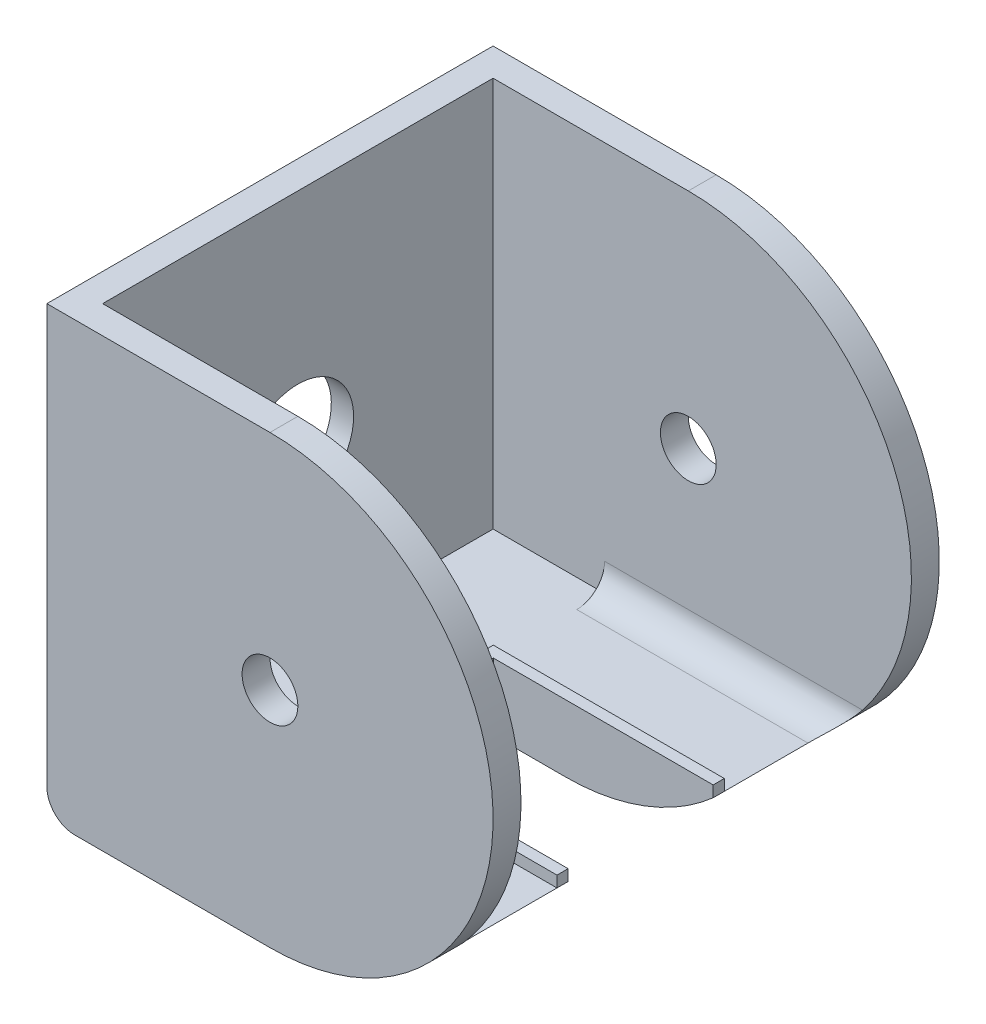
SolidWorks part; units mm, degrees
material "Custom Plastic"
ref_plane "Front Plane" through (0, 0, 0) normal (0, 0, 1) x (1, 0, 0)
ref_plane "Top Plane" through (0, 0, 0) normal (0, 1, 0) x (1, 0, 0)
ref_plane "Right Plane" through (0, 0, 0) normal (1, 0, 0) x (0, 0, -1)
sketch "Sketch1" plane through (0, 0, 0) normal (0, 0, 1) x (1, 0, 0)
  line L0 (72.2954, 0) -> (-7.7046, 0)
  line L1 (-7.7046, -40) -> (32.2954, -40)
  line L2 (-7.7046, -40) -> (-7.7046, 40)
  line L3 (-7.7046, 40) -> (32.2954, 40)
  line L5 (0, 0) -> (-7.7029, 0.3675) construction
  line L6 (0, 0) -> (-7.7029, -0.3675) construction
  arc A0 (-7.7029, 0.3675) -> (-7.7029, -0.3675) centre (32.2954, 0) ccw
  arc A1 (32.2954, -40) -> (32.2954, 40) centre (32.2954, 0) ccw
  circle A2 centre (32.2954, 0) radius 5
  point P0 (0, 0)
  dimension "D3" = 10
  dimension "D1" = 80
  dimension "D2" = 80
extrude "Boss-Extrude1" add sketch "Sketch1" along normal blind 5
sketch "Sketch2" plane through (0, 0, 5) normal (0, 0, 1) x (1, 0, 0)
  line L0 (-7.7046, 40) -> (-2.7046, 40)
  line L1 (-7.7046, 40) -> (32.2954, 40) construction
  line L2 (-2.7046, 40) -> (-2.7046, -40)
  line L3 (-7.7046, -40) -> (32.2954, -40) construction
  line L4 (-2.7046, -40) -> (-7.7046, -40)
  line L5 (-7.7046, -40) -> (-7.7046, 40)
  dimension "D1" = 5
extrude "Boss-Extrude2" add sketch "Sketch2" along normal blind 70
ref_plane "Plane1" through (0, 0, 40) normal (0, 0, 1) x (1, 0, 0)
mirror "Mirror1" about plane through (0, 0, 40) normal (0, 0, 1) of "Boss-Extrude1"
sketch "Sketch4" plane through (0, 0, 5) normal (0, 0, 1) x (1, 0, 0)
  line L0 (-2.7046, -40) -> (-2.7046, -30)
  line L1 (-2.7046, -40) -> (-2.7046, 40) construction
  line L2 (-2.7046, -30) -> (43.4973, -30)
  line L3 (43.4973, -30) -> (58.7529, -30)
  line L4 (-2.7046, -40) -> (32.2954, -40)
  arc A2 (32.2954, -40) -> (58.7529, -30) centre (32.2954, 0) ccw
  dimension "D1" = 10
extrude "Boss-Extrude3" add sketch "Sketch4" along normal blind 70
sketch "Sketch5" plane through (-7.7046, 0, 0) normal (-1, 0, 0) x (0, 0, 1)
  line L0 (0, 40) -> (80, -40)
  circle A0 centre (40, 0) radius 10
  dimension "D1" = 20
extrude "Cut-Extrude1" cut sketch "Sketch5" against normal blind 5 contours L0 A0 | L0 A0
sketch "Sketch6" plane through (-7.7046, 0, 0) normal (-1, 0, 0) x (0, 0, 1)
  circle A0 centre (40, 0) radius 20
  dimension "D1" = 40
extrude "Cut-Extrude2" cut sketch "Sketch6" against normal blind 1
sketch "Sketch7" plane through (0, -30, 0) normal (0, 1, 0) x (1, 0, 0)
  line L1 (-2.7046, -75) -> (-2.7046, -5) construction
  line L2 (58.7529, -75) -> (58.7529, -5) construction
  line L3 (58.7529, -40) -> (58.7529, -27)
  line L4 (58.7529, -27) -> (-2.7046, -27)
  line L5 (-2.7046, -27) -> (-2.7046, -40)
  line L6 (-2.7046, -40) -> (-2.7046, -53)
  line L7 (-2.7046, -53) -> (58.7529, -53)
  line L8 (58.7529, -53) -> (58.7529, -40)
  line L9 (19.3397, -53) -> (19.3397, -27)
  line M10 (58.7529, -75) -> (58.7529, -5)
  dimension "D1" = 13
  dimension "D2" = 13
extrude "Cut-Extrude3" cut sketch "Sketch7" against normal blind 19 contours L9 L7 L4 M10
sketch "Sketch8" plane through (0, -30, 0) normal (0, 1, 0) x (1, 0, 0)
  line L0 (58.7529, -53) -> (19.3397, -53)
  line L1 (19.3397, -53) -> (19.3397, -27)
  line L2 (19.3397, -27) -> (58.7529, -27)
  line L3 (58.7529, -27) -> (58.7529, -25)
  line L5 (58.7529, -55) -> (17.3397, -55)
  line L6 (17.3397, -55) -> (17.3397, -25)
  line L7 (17.3397, -25) -> (56.7529, -25)
  line L8 (58.7529, -55) -> (58.7529, -53)
  line L9 (56.7529, -25) -> (58.7529, -25)
  line L10 (58.7529, -27) -> (58.7529, -24.2721) construction
  line L11 (56.7529, -25) -> (56.7529, -24.2721) construction
  dimension "D1" = 2
extrude "Boss-Extrude4" add sketch "Sketch8" along normal blind 2
fillet "Fillet1" radius 5 3 edges at (-7.7046, -40, 40) (28.0241, -30, 5) (28.0241, -30, 75)
sketch "Sketch9" plane through (0, -30, 0) normal (0, 1, 0) x (1, 0, 0)
  line L0 (-2.7046, -70) -> (-2.7046, -5)
  line L1 (-2.7046, -5) -> (17.2954, -5)
  line L2 (-2.7046, -5) -> (32.2954, -5) construction
  line L3 (17.2954, -5) -> (17.2954, -75)
  line L4 (-2.7046, -70) -> (-2.7046, -75)
  line L5 (-2.7046, -75) -> (17.2954, -75)
  dimension "D1" = 20
extrude "Cut-Extrude4" cut sketch "Sketch9" along normal blind 27
sketch "Sketch10" plane through (0, -30, 0) normal (0, 1, 0) x (1, 0, 0)
  line L1 (13.7954, -52.5) -> (15.7954, -52.5)
  line L4 (13.7954, -52.5) -> (-2.7046, -52.5)
  line L5 (-2.7046, -75) -> (-2.7046, -5) construction
  line L6 (-2.7046, -52.5) -> (-2.7046, -54.5)
  line L7 (-2.7046, -54.5) -> (15.7954, -54.5)
  line L8 (15.7954, -54.5) -> (15.7954, -52.5)
  dimension "D4" = 2
extrude "Boss-Extrude5" add sketch "Sketch10" along normal blind 2
sketch "Sketch11" plane through (0, -30, 0) normal (0, 1, 0) x (1, 0, 0)
  line L0 (-2.7046, -75) -> (-2.7046, -58.25)
  line L1 (-2.7046, -75) -> (-2.7046, -54.5) construction
  line L2 (-2.7046, -58.25) -> (15.8954, -58.25)
  line L3 (15.8954, -58.25) -> (15.8954, -75)
  line L4 (-2.7046, -75) -> (15.8954, -75)
  line L6 (15.8954, -75) -> (17.2954, -75)
  line L7 (17.2954, -75) -> (17.2954, -56.85)
  line L8 (17.2954, -56.85) -> (-2.7046, -56.85)
  line L9 (-2.7046, -75) -> (-2.7046, -5) construction
  line L10 (-2.7046, -56.85) -> (-2.7046, -58.25)
  line M6 (-2.7046, -54.5) -> (-2.7046, -75)
  line M7 (-2.7046, -75) -> (17.2954, -75)
  line M8 (17.2954, -75) -> (17.2954, -70)
  dimension "D1" = 16.75
  dimension "D2" = 18.6
  dimension "D3" = 1.4
extrude "Boss-Extrude6" add sketch "Sketch11" along normal blind 2 contours L7 L8 L2 L3 M6 M7 M8
